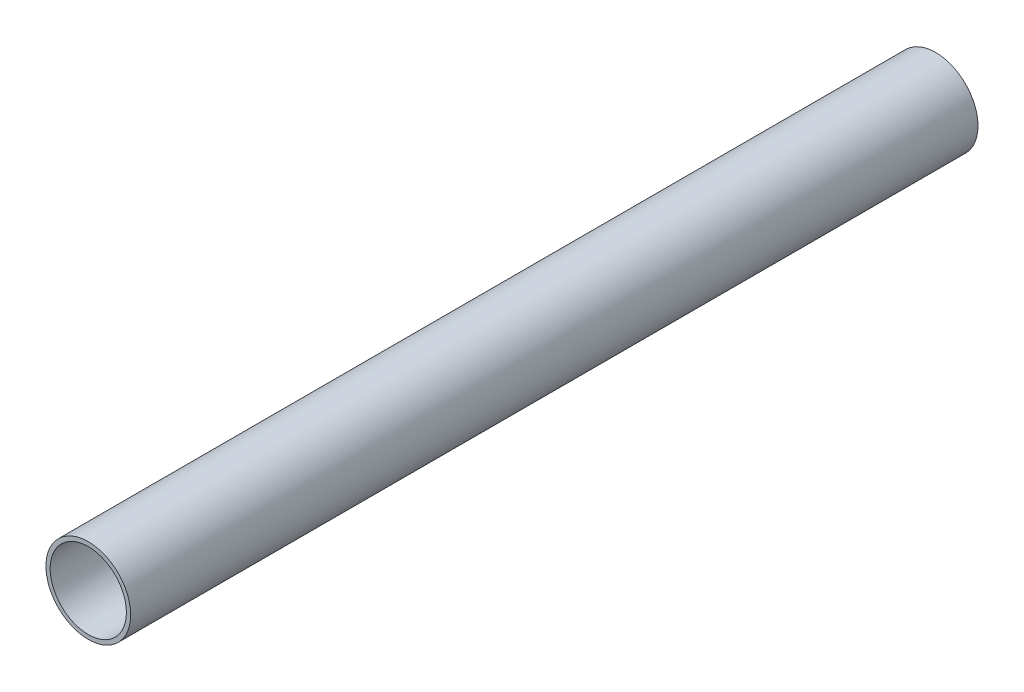
SolidWorks part; units mm, degrees
material "ABS"
ref_plane "Front Plane" through (0, 0, 0) normal (0, 0, 1) x (1, 0, 0)
ref_plane "Top Plane" through (0, 0, 0) normal (0, 1, 0) x (1, 0, 0)
ref_plane "Right Plane" through (0, 0, 0) normal (1, 0, 0) x (0, 0, -1)
sketch "Sketch3" plane through (0, 0, 0) normal (0, 0, 1) x (1, 0, 0)
  circle A0 centre (0, 0) radius 10
  dimension "D1" = 20
extrude "Extrude-Thin2" add sketch "Sketch3" along normal blind 200 thin contours A0 thin type one direction reverse wall 1
